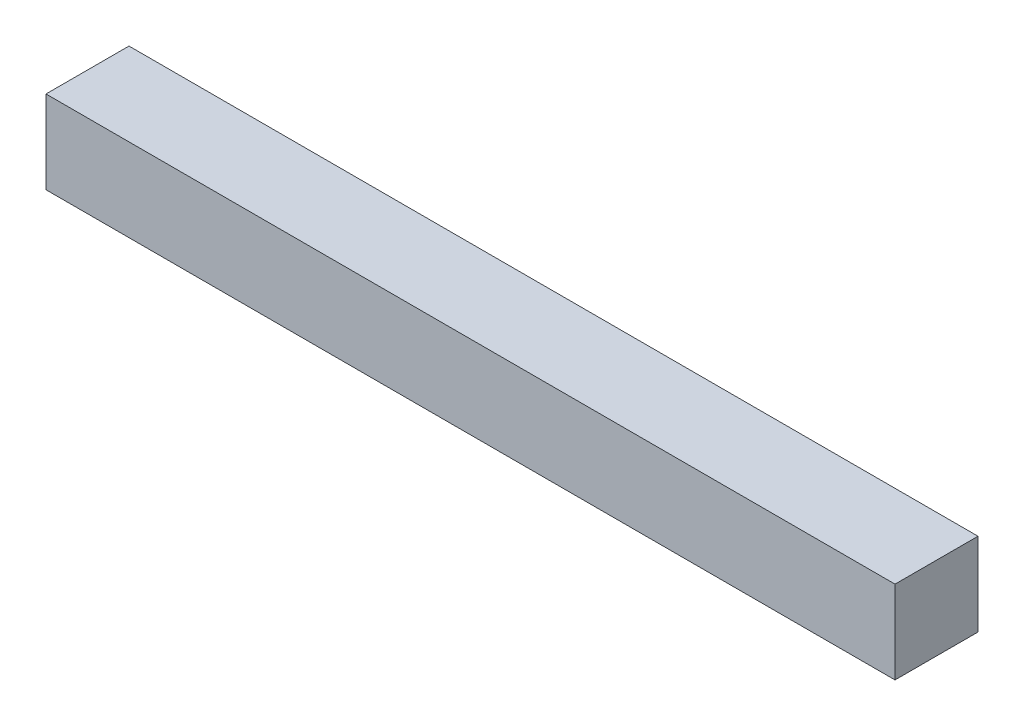
SolidWorks part; units mm, degrees
ref_plane "Plan de face" through (0, 0, 0) normal (0, 0, 1) x (1, 0, 0)
ref_plane "Plan de dessus" through (0, 0, 0) normal (0, 1, 0) x (1, 0, 0)
ref_plane "Plan de droite" through (0, 0, 0) normal (1, 0, 0) x (0, 0, -1)
sketch "Esquisse1" plane through (0, 0, 0) normal (0, 0, 1) x (1, 0, 0)
  line L1 (-70.6069, 40.1724) -> (62.3931, 40.1724)
  line L2 (-70.6069, 40.1724) -> (-70.6069, 27.1724)
  line L3 (-70.6069, 27.1724) -> (62.3931, 27.1724)
  line L4 (62.3931, 40.1724) -> (62.3931, 27.1724)
  dimension "D1" = 13
  dimension "D2" = 133
extrude "Boss.-Extru.1" add sketch "Esquisse1" along normal blind 13
equation "\"EpaisseurPlaque\"= 3"
equation "\"ProfondeurBoite\"=460"
equation "\"LongueurSyphon\"=270"
equation "\"LargeurSyphon\"=120"
equation "\"HauteurCoteDroit\"= 490"
equation "\"HauteurCoteGauche\"= 540"
equation "\"HauteurSolSyphon\"= 300"
equation "\"HauteurSyphon\"=\"HauteurCoteGauche\"-\"HauteurSolSyphon\""
equation "\"LargeurDroite\"=10"
equation "\"LargeurGauche\"=150"
equation "\"LargeurBoite\"= \"LargeurDroite\" + \"LargeurGauche\" + \"LargeurSyphon\""
equation "\"D2@Esquisse1\"=\"LargeurBoite\" - \"LargeurGauche\" + 3"
